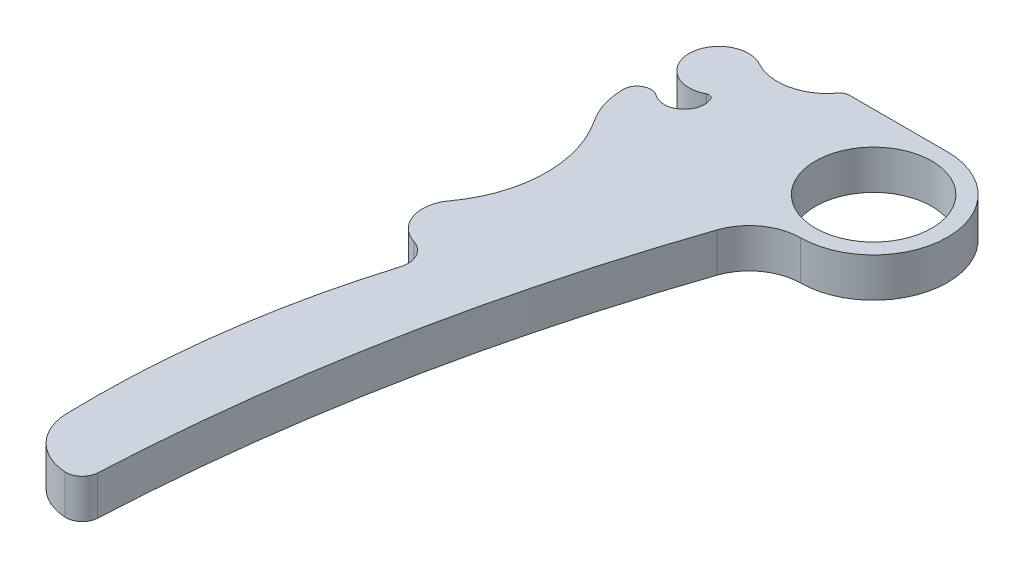
SolidWorks part; units mm, degrees
ref_plane "Alzado" through (0, 0, 0) normal (0, 0, 1) x (1, 0, 0)
ref_plane "Planta" through (0, 0, 0) normal (0, 1, 0) x (1, 0, 0)
ref_plane "Vista lateral" through (0, 0, 0) normal (1, 0, 0) x (0, 0, -1)
sketch "Croquis1" plane through (0, 0, 0) normal (0, 1, 0) x (1, 0, 0)
  line L0 (0, 5.6505) -> (-6.5587, 5.6505)
  line L1 (0, 5.6505) -> (-7.4882, 5.6505)
  circle A0 centre (0, 0) radius 4.4468
  arc A1 (0.0462, -5.6503) -> (0, 5.6505) centre (0, 0) ccw
  arc A2 (-13.007, 4.279) -> (-8.0868, 5.3484) centre (-11.1556, 7.6143) ccw
  arc A3 (-13.007, 4.279) -> (-13.0589, 0.2713) centre (-14.1116, 2.2891) ccw
  arc A4 (-14.8663, -1.7478) -> (-12.5397, 0.0806) centre (-13.9659, -0.499) ccw
  arc A5 (-14.8663, -1.7478) -> (-16.5258, -2.5971) centre (-15.4787, -2.5971) ccw
  arc A6 (-16.5258, -2.5971) -> (-15.5614, -5.7698) centre (-10.8246, -2.5971) ccw
  arc A7 (-15.795, -16.6278) -> (-15.5614, -5.7698) centre (-23.4182, -11.0323) ccw
  arc A8 (-15.795, -16.6278) -> (-14.4674, -20.6639) centre (-13.6911, -18.1721) ccw
  arc A9 (-13.3048, -22.8603) -> (-14.4674, -20.6639) centre (-14.9919, -22.3475) ccw
  arc A10 (-13.3048, -22.8603) -> (-16.335, -45.3552) centre (54.3547, -43.4262) ccw
  arc A11 (-16.335, -45.3552) -> (-12.5314, -49.2414) centre (-12.3365, -45.2461) ccw
  arc A12 (-12.5314, -49.2414) -> (-11.2289, -48.0603) centre (-12.4708, -47.9995) ccw
  arc A13 (-7.4882, 5.6505) -> (-8.0868, 5.3484) centre (-7.4882, 4.9065) ccw
  arc A14 (0.0462, -5.6503) -> (-3.6428, -8.3121) centre (0.0784, -9.5822) ccw
  arc A16 (-3.6428, -8.3121) -> (-11.2289, -48.0603) centre (133.9072, -55.162) ccw
  arc A17 (-12.5397, 0.0806) -> (-13.0589, 0.2713) centre (-12.886, -0.0601) ccw
extrude "Saliente-Extruir1" add sketch "Croquis1" along normal blind 3
